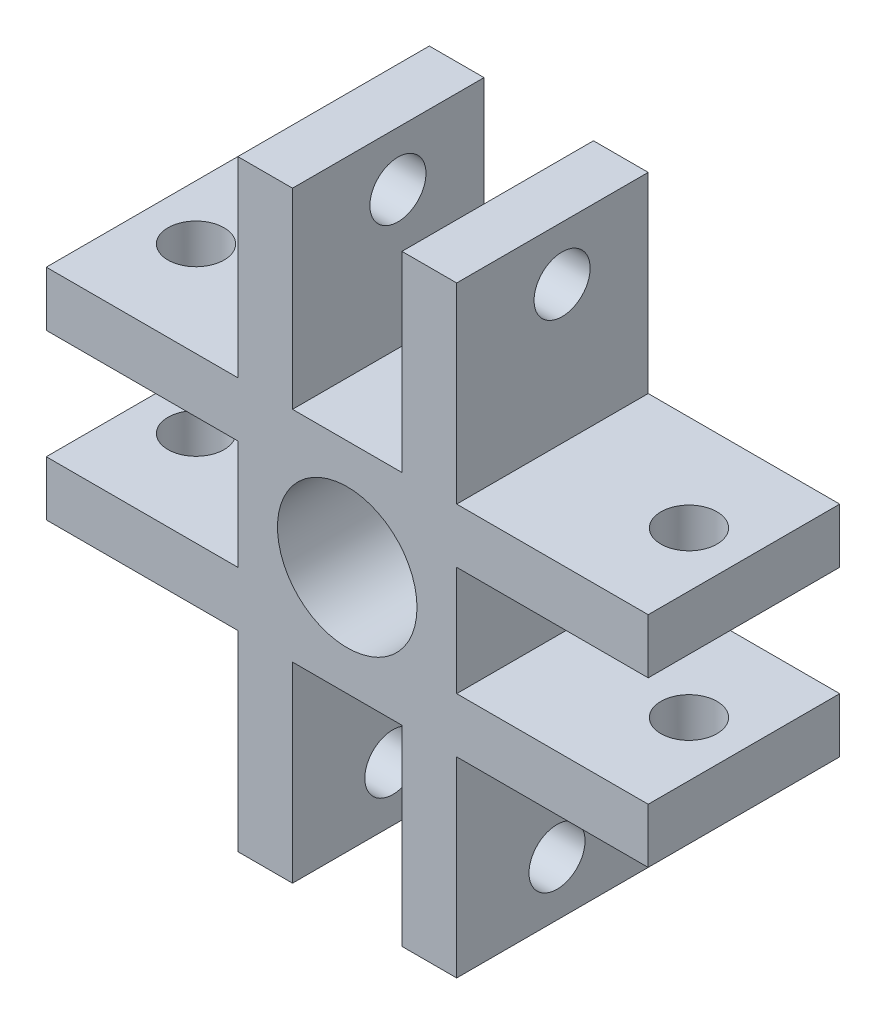
SolidWorks part; units mm, degrees
ref_plane "Front Plane" through (0, 0, 0) normal (0, 0, 1) x (1, 0, 0)
ref_plane "Top Plane" through (0, 0, 0) normal (0, 1, 0) x (1, 0, 0)
ref_plane "Right Plane" through (0, 0, 0) normal (1, 0, 0) x (0, 0, -1)
sketch "Sketch1" plane through (0, 0, 0) normal (0, 0, 1) x (1, 0, 0)
  line L1 (-11, 11) -> (11, 11)
  line L2 (-11, 11) -> (-11, -11)
  line L3 (-11, -11) -> (11, -11)
  line L4 (11, 11) -> (11, -11)
  line L5 (-11, 11) -> (11, -11) construction
  line L6 (-11, -11) -> (11, 11) construction
  point P0 (0, 0)
  dimension "D1" = 22
  dimension "D2" = 22
extrude "Extrude1" add sketch "Sketch1" along normal blind 7
sketch "Sketch2" plane through (0, 0, 7) normal (0, 0, 1) x (1, 0, 0)
  line L0 (11, 11) -> (11, 4)
  line L1 (-11, 11) -> (-4, 11)
  line L2 (-11, 11) -> (-11, 4)
  line L3 (-11, 4) -> (-4, 4)
  line L4 (-4, 11) -> (-4, 4)
  line L5 (4, 4) -> (11, 4)
  line L6 (4, 11) -> (4, 4)
  line L7 (4, 11) -> (11, 11)
  line L8 (-4, -4) -> (-4, -11)
  line L9 (-11, -11) -> (-4, -11)
  line L10 (-11, -4) -> (-11, -11)
  line L11 (-11, -4) -> (-4, -4)
  line L12 (11, -4) -> (11, -11)
  line L13 (4, -11) -> (11, -11)
  line L14 (4, -4) -> (4, -11)
  line L15 (4, -4) -> (11, -4)
  dimension "D1" = 7
  dimension "D2" = 7
extrude "Extrude2" cut sketch "Sketch2" against normal blind 7
sketch "Sketch3" plane through (0, 0, 7) normal (0, 0, 1) x (1, 0, 0)
  line L0 (4, 2) -> (4, -2)
  line L1 (-2, 2) -> (2, 2)
  line L2 (-2, 2) -> (-2, -2)
  line L3 (-2, -2) -> (2, -2)
  line L4 (2, 2) -> (2, -2)
  line L5 (-2, 2) -> (2, -2) construction
  line L6 (-2, -2) -> (2, 2) construction
  line L7 (4, -2) -> (11, -2)
  line L8 (11, -4) -> (11, 4) construction
  line L9 (4, 2) -> (11, 2)
  line L10 (4, 11) -> (4, 4) construction
  line L11 (4, 4) -> (11, 4) construction
  line L12 (11, -4) -> (4, -4) construction
  line L13 (2, -4) -> (2, -11)
  line L14 (-2, -4) -> (-2, -11)
  line L15 (2, -4) -> (-2, -4)
  line L16 (-4, -2) -> (-11, -2)
  line L17 (-4, 2) -> (-11, 2)
  line L18 (-4, -2) -> (-4, 2)
  line L19 (-2, 4) -> (-2, 11)
  line L20 (2, 4) -> (2, 11)
  line L21 (-2, 4) -> (2, 4)
  point P0 (0, 0)
  point P7 (8.43, 0)
  point P9 (11.6726, 0.1646)
  line M2 (11, -4) -> (11, 4)
  line M5 (4, 11) -> (-4, 11)
  line M8 (-11, 4) -> (-11, -4)
  line M11 (-4, -11) -> (4, -11)
  dimension "D1" = 4
  dimension "D2" = 4
  dimension "D3" = 2
  dimension "D4" = 2
extrude "Extrude3" cut sketch "Sketch3" against normal blind 7 contours L16 L18 L17 M8 | L19 L21 L20 M5 | L9 L0 L7 M2 | L13 L15 L14 M11 | L4 L1 L2 L3
sketch "Sketch4" plane through (0, 0, 7) normal (0, 0, 1) x (1, 0, 0)
  line L1 (-2, -2) -> (2, -2)
  line L2 (-2, -2) -> (-2, 2)
  line L3 (-2, 2) -> (2, 2)
  line L4 (2, -2) -> (2, 2)
extrude "Extrude5" add sketch "Sketch4" against normal blind 7
sketch "Sketch5" plane through (0, 0, 7) normal (0, 0, 1) x (1, 0, 0)
  circle A0 centre (0, 0) radius 2.55
  dimension "D1" = 5.1
extrude "Extrude6" cut sketch "Sketch5" against normal blind 10
sketch "Sketch6" plane through (4, 0, 0) normal (1, 0, 0) x (0, 0, -1)
  line L0 (0, 11) -> (0, 4) construction
  line L1 (0, 11) -> (-7, 11) construction
  circle A0 centre (-3.1472, 9.0314) radius 1.025
  point P2 (0, 7.5)
  point P7 (-3.5, 11)
  dimension "D1" = 2.05
  dimension "D2" = 3.5
  dimension "D3" = 2
extrude "Extrude7" cut sketch "Sketch6" against normal blind 10
sketch "Sketch7" plane through (0, -4, 0) normal (0, -1, 0) x (1, 0, 0)
  line L0 (-11, 0) -> (-11, 7) construction
  circle A0 centre (-9, 3.527) radius 1.025
  point P2 (-11, 3.5)
  dimension "D1" = 2.05
  dimension "D2" = 2
extrude "Extrude8" cut sketch "Sketch7" against normal blind 10
sketch "Sketch8" plane through (4, 0, 0) normal (1, 0, 0) x (0, 0, -1)
  line L0 (0, -11) -> (-7, -11) construction
  circle A0 centre (-3.3325, -9) radius 1.025
  point P2 (-3.5, -11)
  dimension "D1" = 2.05
  dimension "D2" = 2
extrude "Extrude9" cut sketch "Sketch8" against normal blind 10
sketch "Sketch9" plane through (0, 4, 0) normal (0, 1, 0) x (1, 0, 0)
  line L0 (11, 0) -> (11, -7) construction
  circle A0 centre (9, -3.5105) radius 1.025
  point P2 (11, -3.5)
  dimension "D1" = 2.05
  dimension "D2" = 2
extrude "Extrude10" cut sketch "Sketch9" against normal blind 10
